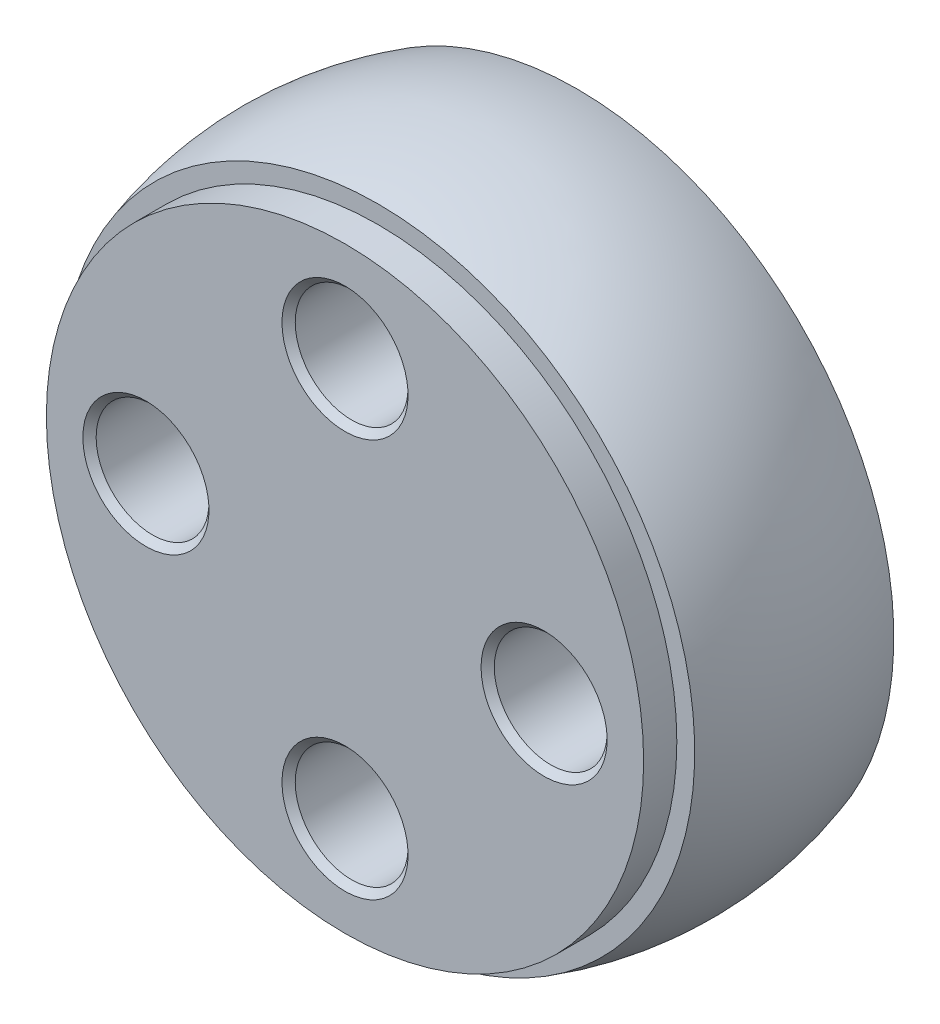
SolidWorks part; units mm, degrees
material "2024-T4"
ref_plane "Спереди" through (0, 0, 0) normal (0, 0, 1) x (1, 0, 0)
ref_plane "Сверху" through (0, 0, 0) normal (0, 1, 0) x (1, 0, 0)
ref_plane "Справа" through (0, 0, 0) normal (1, 0, 0) x (0, 0, -1)
sketch "Эскиз1" plane through (0, 0, 0) normal (1, 0, 0) x (0, 0, -1)
  line L0 (-4, 9) -> (-3, 9)
  line L2 (3, 0) -> (3, 9.5394)
  line L3 (-4, 9) -> (-4, 0)
  line L4 (-3, 9) -> (-3, 9.5394)
  line L5 (0, 0) -> (-4, 0) construction
  line L7 (-4, 0) -> (3, 0)
  arc A0 (-3, 9.5394) -> (3, 9.5394) centre (0, 0) cw
  dimension "D2" = 10
  dimension "D1" = 6
  dimension "D3" = 7
  dimension "D4" = 4
  dimension "D5" = 18
revolve "Повернуть1" add sketch "Эскиз1" angle 360 about L5
hole_wizard "Цековка для винта с внутренним шестигранником M31" positions "Эскиз3" profile "Эскиз2" counterbore size "M3" standard "DIN" end condition through all
sketch "Эскиз3" plane through (0, 0, -3) normal (0, 0, -1) x (-1, 0, 0)
  point P0 (-6, 0)
  point P1 (6, 0)
  point P4 (0, 6)
  point P6 (0, -6)
  dimension "D1" = 12
  dimension "D2" = 12
  dimension "D3" = 6
  dimension "D4" = 6
sketch "Эскиз2" plane through (6, 0, -3) normal (1, 0, 0) x (0, 1, 0)
  line L0 (0, 0) -> (0, 7)
  line L1 (1.7, 6.8) -> (1.9, 7)
  line L2 (1.7, 6.8) -> (1.7, 3.6)
  line L3 (1.7, 3.6) -> (1.9, 3.4)
  line L4 (1.9, 3.4) -> (3, 3.4)
  line L5 (3, 3.4) -> (3, 0.25)
  line L6 (3, 0.25) -> (3.25, 0)
  line L7 (3.25, 0) -> (0, 0)
  line L8 (-3, 0.25) -> (-3.25, 0) construction
  line L9 (-1.7, 3.6) -> (-1.9, 3.4) construction
  line L11 (0, -6.35) -> (0, 107.95) construction
  line L12 (1.9, 7) -> (0, 7)
  line L13 (-1.7, 6.8) -> (-1.9, 7) construction
  dimension "Диаметр сквозного отверстия" = 3.4
  dimension "Глубина сквозного отверстия" = 7
  dimension "Диаметр цековки" = 6
  dimension "Глубина цековки" = 3.4
  dimension "Диаметр передней зенковки" = 6.5
  dimension "Угол передней зенковки" = 90
  dimension "Диаметр средней зенковки" = 3.8
  dimension "Угол средней зенковки" = 90
  dimension "Диаметр задней зенковки" = 3.8
  dimension "Угол задней зенковки" = 90
